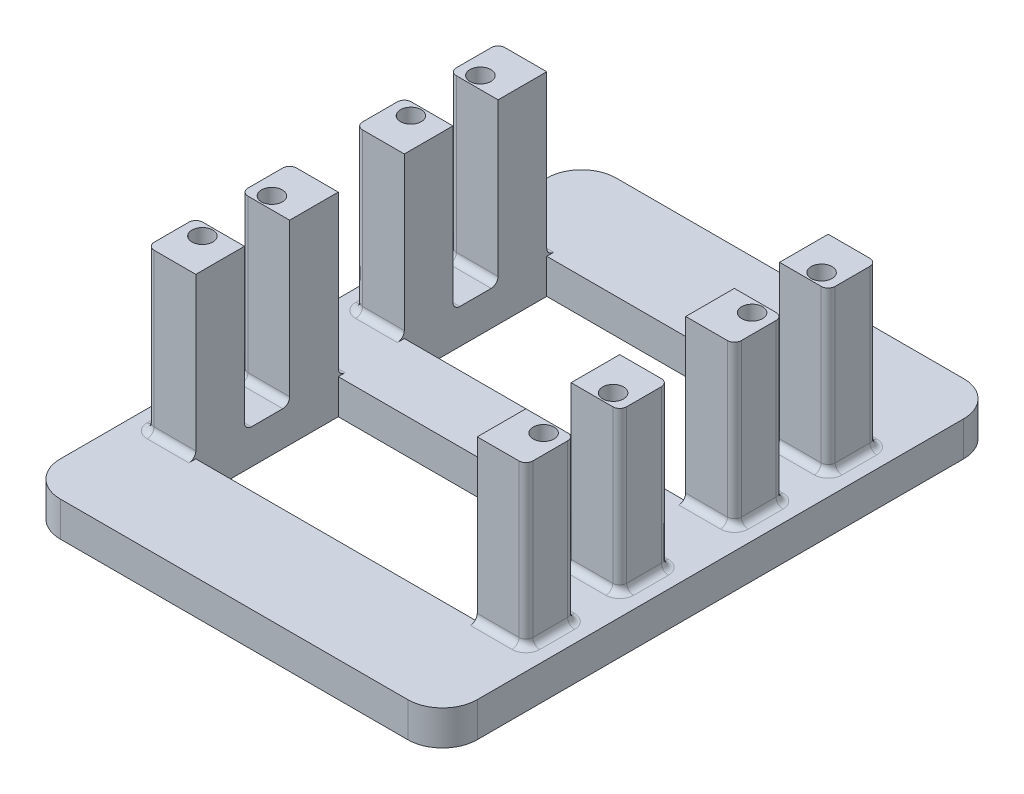
SolidWorks part; units mm, degrees
ref_plane "Front" through (0, 0, 0) normal (0, 0, 1) x (1, 0, 0)
ref_plane "Top" through (0, 0, 0) normal (0, 1, 0) x (1, 0, 0)
ref_plane "Right" through (0, 0, 0) normal (1, 0, 0) x (0, 0, -1)
sketch "草图1" plane through (0, 0, 0) normal (0, 1, 0) x (1, 0, 0)
  line L1 (30, -40) -> (-30, -40)
  line L2 (30, -40) -> (30, 40)
  line L3 (30, 40) -> (-30, 40)
  line L4 (-30, -40) -> (-30, 40)
  line L5 (30, -40) -> (-30, 40) construction
  line L6 (30, 40) -> (-30, -40) construction
  point P0 (0, 0)
  dimension "D1" = 60
  dimension "D2" = 80
extrude "凸台-拉伸1" add sketch "草图1" along normal blind 5
sketch "草图2" plane through (0, 5, 0) normal (0, 1, 0) x (1, 0, 0)
  line L0 (0, 0) -> (0, 40) construction
  line L1 (30, 40) -> (-30, 40) construction
  line L2 (-47.8078, 0) -> (58.4768, 0) construction
  line L3 (20.25, -25.25) -> (-20.25, -25.25)
  line L4 (20.25, 4.75) -> (-20.25, 4.75)
  line L5 (20.25, 4.75) -> (20.25, 25.25)
  line L6 (20.25, 25.25) -> (-20.25, 25.25)
  line L7 (-20.25, 4.75) -> (-20.25, 25.25)
  line L8 (20.25, 4.75) -> (-20.25, 25.25) construction
  line L9 (20.25, 25.25) -> (-20.25, 4.75) construction
  line L10 (-20.25, -4.75) -> (-20.25, -25.25)
  line L11 (20.25, -4.75) -> (-20.25, -4.75)
  line L12 (20.25, -4.75) -> (20.25, -25.25)
  point P7 (0, 15)
  dimension "D1" = 20.5
  dimension "D2" = 40.5
  dimension "D3" = 15
extrude "切除-拉伸1" cut sketch "草图2" against normal through all
sketch "草图3" plane through (0, 5, 0) normal (0, 1, 0) x (1, 0, 0)
  line L0 (0, 0) -> (0, 37.7241) construction
  line L1 (-20.25, 25.25) -> (-27.25, 25.25)
  line L2 (-20.25, 25.25) -> (-20.25, 4.75)
  line L3 (-20.25, 4.75) -> (-27.25, 4.75)
  line L4 (-27.25, 25.25) -> (-27.25, 4.75)
  line L5 (-55.3918, 0) -> (57.4273, 0) construction
  line L6 (20.25, 4.75) -> (27.25, 4.75)
  line L7 (27.25, 25.25) -> (27.25, 4.75)
  line L8 (20.25, 25.25) -> (27.25, 25.25)
  line L9 (20.25, 25.25) -> (20.25, 4.75)
  line L10 (20.25, -25.25) -> (20.25, -4.75)
  line L11 (20.25, -25.25) -> (27.25, -25.25)
  line L12 (27.25, -25.25) -> (27.25, -4.75)
  line L13 (20.25, -4.75) -> (27.25, -4.75)
  line L14 (-20.25, -4.75) -> (-27.25, -4.75)
  line L15 (-27.25, -25.25) -> (-27.25, -4.75)
  line L16 (-20.25, -25.25) -> (-27.25, -25.25)
  line L17 (-20.25, -25.25) -> (-20.25, -4.75)
  dimension "D1" = 7
extrude "凸台-拉伸2" add sketch "草图3" along normal blind 23
sketch "草图4" plane through (0, 28, 0) normal (0, 1, 0) x (1, 0, 0)
  line L0 (-44.4045, 0) -> (59.3141, 0) construction
  line L1 (0, 42.6219) -> (0, -45.2148) construction
  line L2 (-20.25, 4.75) -> (-20.25, 25.25) construction
  line L3 (-27.25, 15) -> (-15.1467, 15) construction
  line L4 (-27.25, 25.25) -> (-27.25, 4.75) construction
  circle A0 centre (-24.55, 20) radius 1.5
  circle A1 centre (-24.55, 10) radius 1.5
  circle A2 centre (24.55, 10) radius 1.5
  circle A3 centre (24.55, 20) radius 1.5
  circle A4 centre (24.55, -10) radius 1.5
  circle A5 centre (24.55, -20) radius 1.5
  circle A6 centre (-24.55, -10) radius 1.5
  circle A7 centre (-24.55, -20) radius 1.5
  dimension "D3" = 3
  dimension "D1" = 4.3
  dimension "D2" = 10
extrude "切除-拉伸2" cut sketch "草图4" against normal blind 10
fillet "圆角1" radius 5 4 edges at (-30, 2.5, -40) (30, 2.5, -40) (30, 2.5, 40) (-30, 2.5, 40)
sketch "草图6" plane through (0, 28, 0) normal (0, 1, 0) x (1, 0, 0)
  line L0 (20.25, 15) -> (-54.7098, 15) construction
  line L1 (20.25, 25.25) -> (20.25, 4.75) construction
  line L2 (-40.7965, 0) -> (45.2044, 0) construction
  line L3 (0, 0) -> (0, 42.5294) construction
  line L4 (-27.25, 25.25) -> (-27.25, 4.75) construction
  line L5 (-20.25, 11.75) -> (-27.25, 11.75)
  line L6 (-20.25, 11.75) -> (-20.25, 18.25)
  line L7 (-20.25, 18.25) -> (-27.25, 18.25)
  line L8 (-27.25, 11.75) -> (-27.25, 18.25)
  line L9 (-20.25, 11.75) -> (-27.25, 18.25) construction
  line L10 (-20.25, 18.25) -> (-27.25, 11.75) construction
  line L11 (20.25, 18.25) -> (27.25, 18.25)
  line L12 (27.25, 11.75) -> (27.25, 18.25)
  line L13 (20.25, 11.75) -> (27.25, 11.75)
  line L14 (20.25, 11.75) -> (20.25, 18.25)
  line L15 (20.25, -11.75) -> (20.25, -18.25)
  line L16 (20.25, -11.75) -> (27.25, -11.75)
  line L17 (27.25, -11.75) -> (27.25, -18.25)
  line L18 (20.25, -18.25) -> (27.25, -18.25)
  line L19 (-20.25, -18.25) -> (-27.25, -18.25)
  line L20 (-27.25, -11.75) -> (-27.25, -18.25)
  line L21 (-20.25, -11.75) -> (-27.25, -11.75)
  line L22 (-20.25, -11.75) -> (-20.25, -18.25)
  point P9 (-23.75, 15)
  point P16 (-23.75, 11.75)
  dimension "D1" = 7
  dimension "D2" = 0
  dimension "D3" = 6.5
extrude "切除-拉伸9" cut sketch "草图6" against normal blind 23
fillet "圆角4" radius 1 16 edges at (27.25, 16.5, -25.25) (27.25, 16.5, -18.25) (27.25, 16.5, -11.75) (27.25, 16.5, -4.75) (27.25, 16.5, 4.75) (27.25, 16.5, 11.75) (27.25, 16.5, 18.25) (27.25, 16.5, 25.25) (-27.25, 16.5, 18.25) (-27.25, 16.5, 25.25) (-27.25, 16.5, 4.75) (-27.25, 16.5, 11.75) (-27.25, 16.5, -25.25) (-27.25, 16.5, -11.75) (-27.25, 16.5, -4.75) (-27.25, 16.5, -18.25)
fillet "圆角6" radius 1 40 edges at (23.25, 5, -18.25) (26.9571, 5, -18.5429) (23.25, 5, -25.25) (26.9571, 5, -24.9571) (23.25, 5, -4.75) (26.9571, 5, -5.0429) (23.25, 5, -11.75) (26.9571, 5, -11.4571) (23.25, 5, 11.75) (26.9571, 5, 11.4571) (23.25, 5, 4.75) (26.9571, 5, 5.0429) (23.25, 5, 25.25) (26.9571, 5, 24.9571) (23.25, 5, 18.25) (26.9571, 5, 18.5429) (-23.25, 5, 18.25) (-26.9571, 5, 18.5429) (-23.25, 5, 25.25) (-26.9571, 5, 24.9571) (-23.25, 5, 4.75) (-26.9571, 5, 5.0429) (-23.25, 5, 11.75) (-26.9571, 5, 11.4571) (-23.25, 5, -11.75) (-26.9571, 5, -11.4571) (-23.25, 5, -4.75) (-26.9571, 5, -5.0429) (-23.25, 5, -25.25) (-26.9571, 5, -24.9571) (-23.25, 5, -18.25) (-26.9571, 5, -18.5429) (27.25, 5, -21.75) (27.25, 5, -8.25) (27.25, 5, 8.25) (27.25, 5, 21.75) (-27.25, 5, 21.75) (-27.25, 5, 8.25) (-27.25, 5, -8.25) (-27.25, 5, -21.75)
